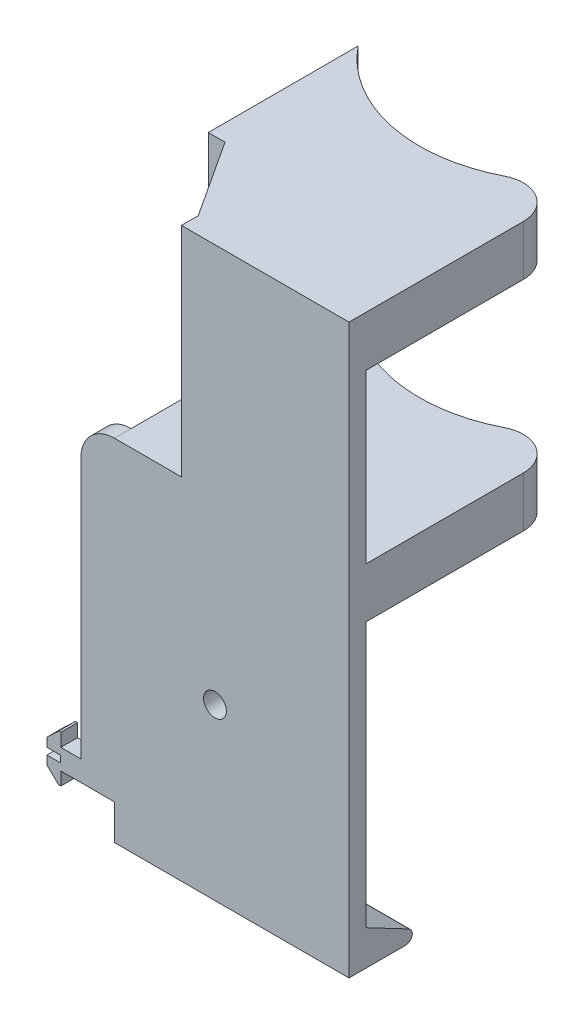
SolidWorks part; units mm, degrees
ref_plane "Front Plane" through (0, 0, 0) normal (0, 0, 1) x (1, 0, 0)
ref_plane "Top Plane" through (0, 0, 0) normal (0, 1, 0) x (1, 0, 0)
ref_plane "Right Plane" through (0, 0, 0) normal (1, 0, 0) x (0, 0, -1)
sketch "Sketch2" plane through (0, 0, 0) normal (0, 0, 1) x (1, 0, 0)
  line L1 (-5.1524, -3.6183) -> (-1.6411, -6.95)
  line L2 (-1.6411, -6.95) -> (-1, -6.95)
  line L6 (-5.1524, -3.6183) -> (-5.1524, 3.6183)
  line L7 (-1, -6.95) -> (-1, 6.95)
  line L8 (0, 0) -> (-6.1524, 0) construction
  line L9 (-1.6411, 6.95) -> (-1, 6.95)
  line L10 (-5.1524, 3.6183) -> (-1.6411, 6.95)
  line L11 (-1, -3.05) -> (5, -3.05)
  line L12 (-1, 3.05) -> (5, 3.05)
  line L13 (5, -3.05) -> (95, -3.05)
  line L14 (5, 3.05) -> (5, 155.95)
  line L15 (5, 155.95) -> (95, 155.95)
  line L16 (95, 155.95) -> (95, -3.05)
  line L17 (-1, 3.05) -> (-1, -3.05)
  point P11 (-1, 0)
  point P13 (-5.1524, 0)
  line B0 (0, -7.95) -> (-2.04, -7.95)
  line B1 (-6.1524, -4.048) -> (-6.1524, 4.048)
  line B2 (-2.04, 7.95) -> (0, 7.95)
  line B3 (0, 7.95) -> (0, -7.95)
  line B4 (-2.04, -7.95) -> (-6.1524, -4.048)
  line B5 (-6.1524, 4.048) -> (-2.04, 7.95)
  line B6 (0, -4.05) -> (0, 4.05) construction
  dimension "D1" = 1
  dimension "D2" = 1
  dimension "D3" = 1
  dimension "D4" = 1
  dimension "D5" = 1
  dimension "D6" = 6
  dimension "D7" = 90
  dimension "D8" = 159
sketch_block_instance "Extrusion Profile-2"
sketch_block "Block1" parameters "D1"=8.44, "D2"=2.6, "D3"=6, "D4"=16.7, "D6"=5.6686, "D7"=2.0404, "D8"=8.0963, "D9"=15.9, "D5"=2.4157
extrude "Boss-Extrude1" add sketch "Sketch2" against normal blind 5 contours L8 L17 L7 L9 L10 L6 | L7 L8 L6 L1 L2 | L12 B3 L11 L13 L16 L15 L14 | B3 L8 L7 L11 | L8 B3 L12 L17
sketch "Sketch3" plane through (0, 155.95, 0) normal (0, 1, 0) x (1, 0, 0)
  line L0 (5, 5) -> (5, 0) construction
  line L1 (95, 5) -> (95, 0) construction
  line L2 (5, 101) -> (95, 101) construction
  line L3 (15, 72.7157) -> (15, 5)
  line L4 (5, 5) -> (95, 5) construction
  line L5 (15, 5) -> (85, 5)
  line L6 (50, 0) -> (50, -5.3878) construction
  line L7 (5, 0) -> (95, 0) construction
  line L8 (85, 72.7157) -> (85, 5)
  arc A0 (5, 101) -> (95, 101) centre (50, 101) ccw
  arc A1 (15, 72.7157) -> (85, 72.7157) centre (50, 101) ccw
  line M7 (95, 5) -> (5, 5)
  dimension "D1" = 45
  dimension "D2" = 96
  dimension "D3" = 35
extrude "Boss-Extrude2" add sketch "Sketch3" against normal blind 80 contours A0 L3 L8 M7
sketch "Sketch4" plane through (0, 0, 0) normal (0, 0, 1) x (1, 0, 0)
  line L0 (-5.1524, 1) -> (-5.1524, -1)
  line L1 (-5.1524, -3.6183) -> (-5.1524, 3.6183) construction
  line L2 (-5.1524, -1) -> (-1.1524, -1)
  line L3 (-1.1524, -1) -> (-1.1524, 1)
  line L4 (-1.1524, 1) -> (-5.1524, 1)
  point P5 (-5.1524, 0)
  dimension "D1" = 2
  dimension "D2" = 4
extrude "Cut-Extrude1" cut sketch "Sketch4" against normal through all
sketch "Sketch5" plane through (15, 0, 0) normal (-1, 0, 0) x (0, 0, 1)
  line L0 (-5, 3.05) -> (-5, 155.95) construction
  line L1 (-5, 140.95) -> (-72.7157, 140.95)
  line L2 (-5, 140.95) -> (-5, 90.95)
  line L3 (-5, 90.95) -> (-72.7157, 90.95)
  line L4 (-72.7157, 140.95) -> (-72.7157, 90.95)
  line L5 (-72.7157, 75.95) -> (-72.7157, 155.95) construction
  line L6 (-72.7157, 155.95) -> (-5, 155.95) construction
  line L7 (-72.7157, 75.95) -> (-5, 75.95) construction
  dimension "D1" = 15
  dimension "D2" = 15
extrude "Cut-Extrude2" cut sketch "Sketch5" against normal through all
sketch "Sketch6" plane through (0, 155.95, 0) normal (0, 1, 0) x (1, 0, 0)
  line L0 (35, 0) -> (35, 5)
  line L1 (5, 0) -> (95, 0) construction
  line L2 (35, 5) -> (20, 28)
  line L3 (20, 28) -> (15, 28)
  line L4 (15, 72.7157) -> (15, 5) construction
  line L5 (15, 28) -> (15, 5)
  line L6 (15, 5) -> (5, 5)
  line L7 (5, 5) -> (5, 0)
  line L8 (5, 0) -> (35, 0)
  point P4 (35.7814, 0)
  dimension "D1" = 5
  dimension "D2" = 23
  dimension "D3" = 30
extrude "Cut-Extrude3" cut sketch "Sketch6" against normal blind 65
sketch "Sketch7" plane through (0, -3.05, 0) normal (0, -1, 0) x (1, 0, 0)
  line L1 (95, 0) -> (15, 0)
  line L2 (95, 0) -> (95, -5)
  line L3 (95, -5) -> (15, -5)
  line L4 (15, 0) -> (15, -5)
extrude "Boss-Extrude3" add sketch "Sketch7" along normal blind 10.5
sketch "Sketch8" plane through (15, 0, 0) normal (-1, 0, 0) x (0, 0, 1)
  line L0 (-5, -3.05) -> (-25, -13.55)
  line L1 (-25, -13.55) -> (-5, -13.55)
  line L2 (-5, -3.05) -> (-5, -13.55)
  dimension "D1" = 20
extrude "Boss-Extrude4" add sketch "Sketch8" against normal up to surface (80 mm away) up to face at (95, 71.2, -2.5)
fillet "Fillet1" radius 2 1 edges at (55, -13.55, -25)
fillet "Fillet2" radius 10 1 edges at (5, 90.95, -2.5)
sketch "Sketch9" plane through (0, 155.95, 0) normal (0, 1, 0) x (1, 0, 0)
  line L0 (85, 5) -> (85, 0)
  line L1 (35, 0) -> (95, 0) construction
  line L2 (85, 0) -> (95, 0)
  line L3 (95, 0) -> (95, 72.7157)
  line L4 (95, 72.7157) -> (85, 72.7157)
  line L5 (85, 72.7157) -> (85, 5) construction
  line L6 (85, 72.7157) -> (85, 5)
  arc A0 (15, 72.7157) -> (85, 72.7157) centre (50, 101) ccw construction
extrude "Cut-Extrude4" cut sketch "Sketch9" against normal through all
fillet "Fillet3" radius 10 1 edges at (85, 83.45, -72.7157)
sketch "Sketch10" plane through (0, 0, -5) normal (0, 0, -1) x (-1, 0, 0)
  circle A0 centre (-45, 37.0769) radius 3.4
  dimension "D1" = 6.8
extrude "Cut-Extrude5" cut sketch "Sketch10" against normal through all
